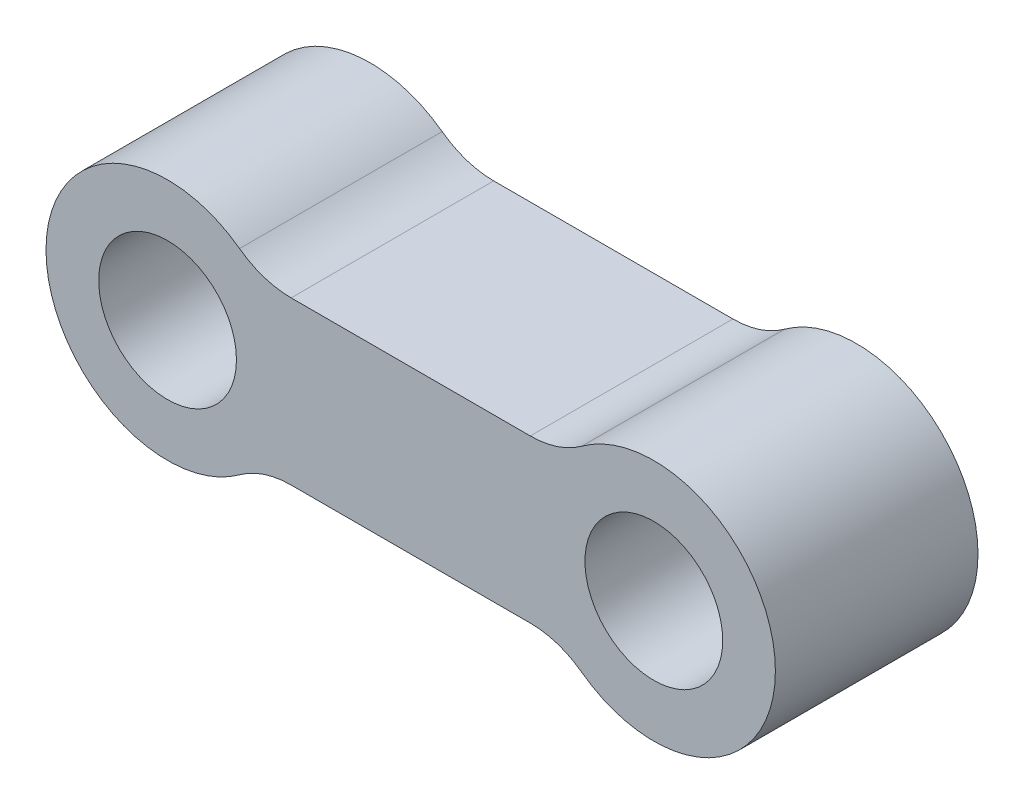
SolidWorks part; units mm, degrees
ref_plane "Alzado" through (0, 0, 0) normal (0, 0, 1) x (1, 0, 0)
ref_plane "Planta" through (0, 0, 0) normal (0, 1, 0) x (1, 0, 0)
ref_plane "Vista lateral" through (0, 0, 0) normal (1, 0, 0) x (0, 0, -1)
sketch "Croquis1" plane through (0, 0, 0) normal (0, 0, 1) x (1, 0, 0)
  line L0 (-15, 0) -> (15, 0) construction
  line L1 (0, 8.3888) -> (0, 0) construction
  line L2 (-7.3777, -5) -> (7.3777, -5)
  line L3 (-7.3777, 5) -> (7.3777, 5)
  circle A0 centre (-15, 0) radius 4.25
  arc A1 (-10.5581, 6.0431) -> (-10.5581, -6.0431) centre (-15, 0) ccw
  arc A2 (10.5581, -6.0431) -> (10.5581, 6.0431) centre (15, 0) ccw
  circle A3 centre (15, 0) radius 4.25
  arc A4 (-10.5581, 6.0431) -> (-7.3777, 5) centre (-7.3777, 10.3699) ccw
  arc A5 (10.5581, 6.0431) -> (7.3777, 5) centre (7.3777, 10.3699) cw
  arc A6 (10.5581, -6.0431) -> (7.3777, -5) centre (7.3777, -10.3699) ccw
  arc A7 (-10.5581, -6.0431) -> (-7.3777, -5) centre (-7.3777, -10.3699) cw
  point P3 (0, 0)
  dimension "D2" = 15
  dimension "D4" = 8.5
  dimension "D5" = 8.5
  dimension "D6" = 5
  dimension "D1" = 30
extrude "Saliente-Extruir1" add sketch "Croquis1" along normal blind 12.5
